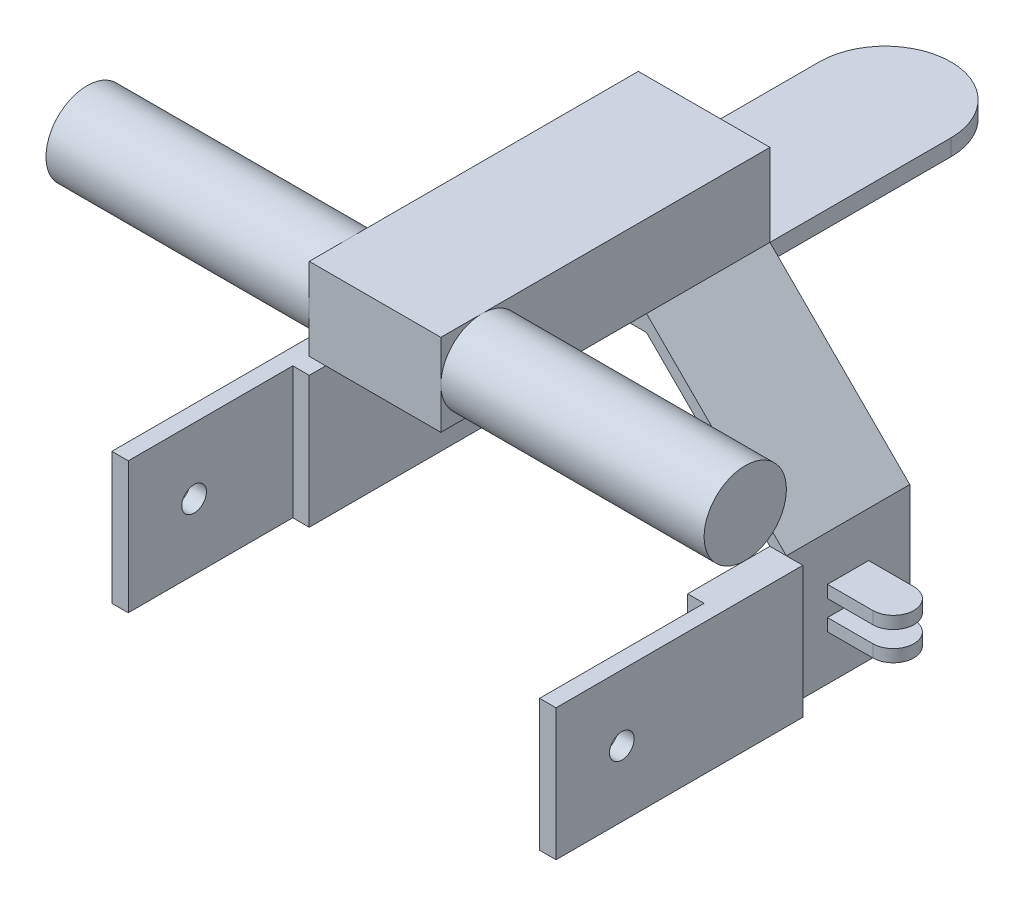
SolidWorks part; units mm, degrees
ref_plane "Front" through (0, 0, 0) normal (0, 0, 1) x (1, 0, 0)
ref_plane "Top" through (0, 0, 0) normal (0, 1, 0) x (1, 0, 0)
ref_plane "Right" through (0, 0, 0) normal (1, 0, 0) x (0, 0, -1)
sketch "草图1" plane through (0, 0, 0) normal (0, 0, 1) x (1, 0, 0)
  line L0 (-50, 16) -> (-16, 50)
  line L5 (-46, 0) -> (46, 0) construction
  line L6 (-46, 0) -> (-46, 46) construction
  line L7 (-46, 46) -> (46, 46) construction
  line L8 (46, 0) -> (46, 46) construction
  line L10 (-46, 16) -> (-46, -16)
  line L11 (-46, -16) -> (-50, -16)
  line L12 (-50, 16) -> (-50, -16)
  line L14 (46, 16) -> (46, -16)
  line L15 (46, -16) -> (50, -16)
  line L16 (50, 16) -> (50, -16)
  line L17 (-16, 46) -> (16, 46)
  line L19 (-16, 50) -> (16, 50)
  line L21 (-46, 16) -> (-16, 46)
  line L22 (46, 16) -> (16, 46)
  line L23 (50, 16) -> (16, 50)
  dimension "D1" = 92
  dimension "D2" = 46
  dimension "D3" = 46
  dimension "D4" = 32
  dimension "D5" = 16
  dimension "D6" = 4
  dimension "D7" = 32
  dimension "D8" = 4
  dimension "D9" = 16
  dimension "D10" = 32
  dimension "D11" = 4
extrude "凸台-拉伸1" add sketch "草图1" along normal blind 30
sketch "草图2" plane through (0, 0, 0) normal (0, 0, -1) x (-1, 0, 0)
  line L1 (-16, 50) -> (16, 50)
  line L2 (-16, 50) -> (-16, 46)
  line L3 (-16, 46) -> (16, 46)
  line L4 (16, 50) -> (16, 46)
extrude "凸台-拉伸2" add sketch "草图2" along normal blind 60
sketch "草图3" plane through (0, 50, 0) normal (0, 1, 0) x (1, 0, 0)
  line L2 (-16, 44) -> (-16, 67.2266)
  line L3 (-16, 67.2266) -> (16, 67.2266)
  line L4 (16, 44) -> (16, 67.2266)
  arc A0 (16, 44) -> (-16, 44) centre (0, 44) ccw
extrude "切除-拉伸1" cut sketch "草图3" against normal blind 30
sketch "草图6" plane through (0, 0, 30) normal (0, 0, 1) x (1, 0, 0)
  line L0 (50, -16) -> (50, 16) construction
  line L1 (-50, -16) -> (-46, -16)
  line L2 (-50, -16) -> (-50, 16)
  line L3 (-50, 16) -> (-46, 16)
  line L4 (-46, -16) -> (-46, 16)
  line L5 (46, -16) -> (50, -16)
  line L6 (46, -16) -> (46, 16)
  line L7 (46, 16) -> (50, 16)
  line L8 (50, -16) -> (50, 16)
extrude "凸台-拉伸4" add sketch "草图6" along normal blind 20
sketch "草图7" plane through (0, 16, 0) normal (0, 1, 0) x (1, 0, 0)
  line L1 (-50, -30) -> (-54, -30)
  line L2 (-50, -30) -> (-50, -90)
  line L3 (-50, -90) -> (-54, -90)
  line L4 (-54, -30) -> (-54, -90)
  line L5 (50, -30) -> (54, -30)
  line L6 (50, -30) -> (50, -90)
  line L7 (50, -90) -> (54, -90)
  line L8 (54, -30) -> (54, -90)
  dimension "D1" = 60
  dimension "D2" = 4
  dimension "D3" = 4
  dimension "D4" = 60
extrude "凸台-拉伸5" add sketch "草图7" against normal blind 32
sketch "草图8" plane through (-54, 0, 0) normal (-1, 0, 0) x (0, 0, 1)
  line L0 (90, 0) -> (0, 0) construction
  line L1 (90, -16) -> (90, 16) construction
  circle A0 centre (74, 0) radius 3
  dimension "D1" = 16
extrude "切除-拉伸3" cut sketch "草图8" against normal through all
sketch "草图9" plane through (0, 50, 0) normal (0, 1, 0) x (1, 0, 0)
  line L1 (-16, 0) -> (16, 0)
  line L2 (-16, 0) -> (-16, -80)
  line L3 (-16, -80) -> (16, -80)
  line L4 (16, 0) -> (16, -80)
  dimension "D1" = 80
  dimension "D2" = 32
extrude "凸台-拉伸6" add sketch "草图9" along normal blind 20
sketch "草图10" plane through (0, 0, 0) normal (1, 0, 0) x (0, 0, -1)
  circle A0 centre (-70, 60) radius 10
extrude "凸台-拉伸7" add sketch "草图10" along normal mid plane 160
sketch "草图11" plane through (50, 0, 0) normal (1, 0, 0) x (0, 0, -1)
  line L0 (0, 0) -> (-90, 0) construction
  line L1 (-90, -16) -> (-90, 16) construction
  line L2 (-15, 16) -> (-15, -16) construction
  line L3 (-30, 16) -> (0, 16) construction
  line L4 (-30, -16) -> (0, -16) construction
  line L5 (-20, -2) -> (-20, -5)
  line L6 (-20, 5) -> (-10, 5)
  line L7 (-20, 5) -> (-20, 2)
  line L8 (-20, -5) -> (-10, -5)
  line L9 (-10, 5) -> (-10, 2)
  line L10 (-20, 2) -> (-10, 2)
  line L12 (-20, -2) -> (-10, -2)
  line L14 (-10, -2) -> (-10, -5)
  dimension "D1" = 10
  dimension "D2" = 10
  dimension "D3" = 5
  dimension "D4" = 5
  dimension "D5" = 4
  dimension "D6" = 2
extrude "凸台-拉伸8" add sketch "草图11" along normal blind 16
sketch "草图12" plane through (0, 5, 0) normal (0, 1, 0) x (1, 0, 0)
  line L1 (61, -10) -> (68.714, -10)
  line L3 (61, -20) -> (68.714, -20)
  line L4 (68.714, -10) -> (68.714, -20)
  arc A0 (61, -20) -> (61, -10) centre (61, -15) ccw
extrude "切除-拉伸4" cut sketch "草图12" against normal blind 16
